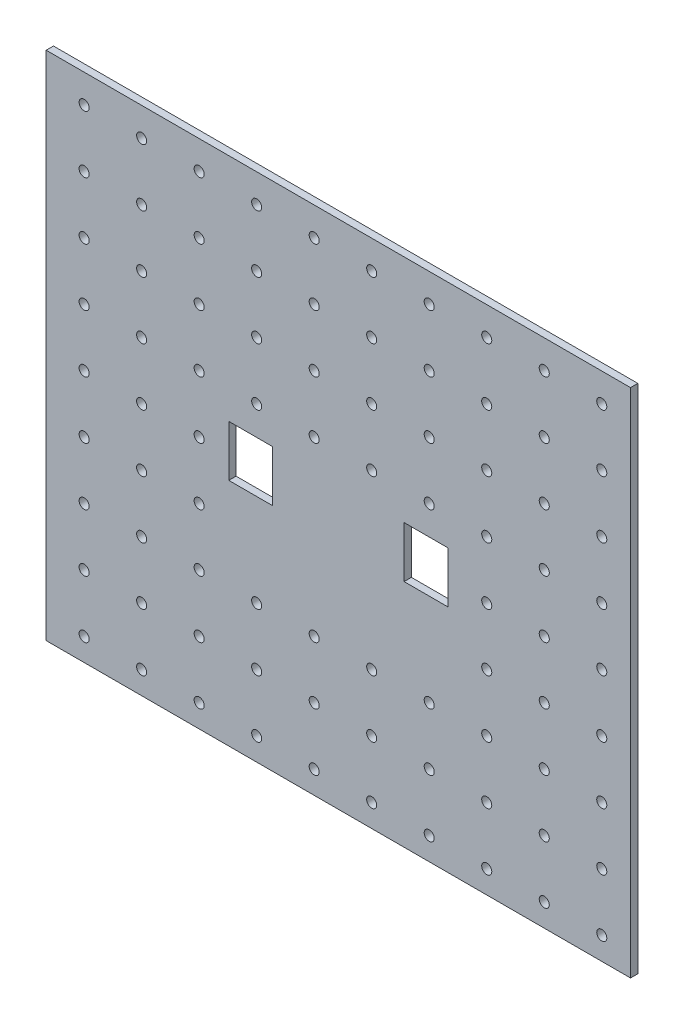
SolidWorks part; units mm, degrees
ref_plane "Front Plane" through (0, 0, 0) normal (0, 0, 1) x (1, 0, 0)
ref_plane "Top Plane" through (0, 0, 0) normal (0, 1, 0) x (1, 0, 0)
ref_plane "Right Plane" through (0, 0, 0) normal (1, 0, 0) x (0, 0, -1)
sketch "Sketch1" plane through (0, 0, 0) normal (0, 0, 1) x (1, 0, 0)
  line L0 (0, 88.9) -> (0, -88.9) construction
  line L1 (-101.6, -88.9) -> (101.6, -88.9)
  line L2 (-101.6, -88.9) -> (-101.6, 88.9)
  line L3 (-101.6, 88.9) -> (101.6, 88.9)
  line L4 (101.6, -88.9) -> (101.6, 88.9)
  line L5 (-101.6, -88.9) -> (101.6, 88.9) construction
  line L6 (-101.6, 88.9) -> (101.6, -88.9) construction
  line L7 (-38.1, 8.89) -> (-22.86, 8.89)
  line L8 (-38.1, 8.89) -> (-38.1, -8.89)
  line L9 (-38.1, -8.89) -> (-22.86, -8.89)
  line L10 (-22.86, 8.89) -> (-22.86, -8.89)
  line L11 (-38.1, 8.89) -> (-22.86, -8.89) construction
  line L12 (-38.1, -8.89) -> (-22.86, 8.89) construction
  line L13 (38.1, -8.89) -> (22.86, -8.89)
  line L14 (22.86, 8.89) -> (22.86, -8.89)
  line L15 (38.1, 8.89) -> (22.86, 8.89)
  line L16 (38.1, 8.89) -> (38.1, -8.89)
  point P0 (0, 0)
  point P6 (-30.48, 0)
  point P12 (-101.6, 0)
  dimension "D1" = 177.8
  dimension "D2" = 203.2
  dimension "D3" = 17.78
  dimension "D4" = 15.24
  dimension "D5" = 71.12
extrude "Boss-Extrude1" add sketch "Sketch1" along normal blind 2.54
sketch "Sketch2" plane through (0, 0, 0) normal (0, 0, -1) x (-1, 0, 0)
  line L0 (-101.6, -88.9) -> (-101.6, 88.9) construction
  line L1 (-101.6, 88.9) -> (101.6, 88.9) construction
  circle A0 centre (-91.6, 78.994) radius 1.75
  point P4 (0, 0)
  dimension "D1" = 3.5
  dimension "D2" = 10
  dimension "D3" = 9.906
sketch "Sketch3" plane through (0, 0, 0) normal (0, 0, -1) x (-1, 0, 0)
  point P0 (-91.6, 78.994)
hole_wizard "M2.5 Clearance Hole1" positions "Sketch3" profile "Sketch4" hole size "M2.5" standard "ANSI Metric"
sketch "Sketch4" plane through (91.6, 78.994, 0) normal (1, 0, 0) x (0, 1, 0)
  line L0 (0, 0) -> (0, 5.6235)
  line L1 (0, 5.6235) -> (1.75, 4.572)
  line L2 (1.75, 4.572) -> (1.75, 0)
  line L5 (1.75, 0) -> (0, 0)
  line L10 (0, 5.6235) -> (-1.75, 4.572) construction
  line L11 (0, -6.35) -> (0, 107.95) construction
  dimension "Hole Dia." = 3.5
  dimension "Hole Depth" = 4.572
  dimension "Drill Angle" = 118
pattern_linear "LPattern2" count 9 spacing 20 along (0, -1, 0) count 10 spacing 20 along (-1, 0, 0) skipping (4, 3), (4, 4), (4, 5), (4, 6), (5, 3), (5, 4), (5, 5), (5, 6) of "M2.5 Clearance Hole1"
